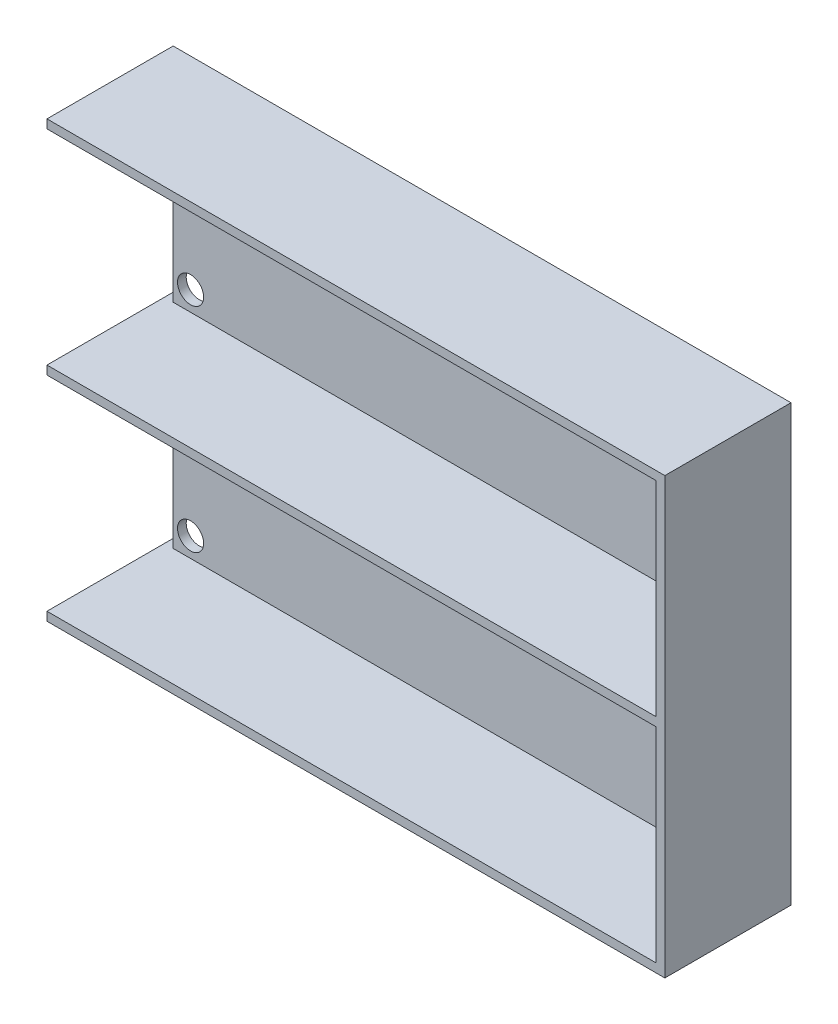
SolidWorks part; units mm, degrees
ref_plane "Front Plane" through (0, 0, 0) normal (0, 0, 1) x (1, 0, 0)
ref_plane "Top Plane" through (0, 0, 0) normal (0, 1, 0) x (1, 0, 0)
ref_plane "Right Plane" through (0, 0, 0) normal (1, 0, 0) x (0, 0, -1)
sketch "Sketch1" plane through (0, 0, 0) normal (0, 0, 1) x (1, 0, 0)
  line L1 (-62.5513, 46.7897) -> (79.4487, 46.7897)
  line L2 (-62.5513, 46.7897) -> (-62.5513, -53.2103)
  line L3 (-62.5513, -53.2103) -> (79.4487, -53.2103)
  line L4 (79.4487, 46.7897) -> (79.4487, -53.2103)
  dimension "D1" = 142
  dimension "D2" = 100
extrude "Boss-Extrude1" add sketch "Sketch1" along normal blind 2
sketch "Sketch3" plane through (0, 0, 2) normal (0, 0, 1) x (1, 0, 0)
  line L0 (79.4487, -53.2103) -> (79.4487, 46.7897) construction
  line L1 (-62.5513, -53.2103) -> (79.4487, -53.2103)
  line L2 (-62.5513, -53.2103) -> (-62.5513, -51.2103)
  line L3 (-62.5513, -51.2103) -> (77.4487, -51.2103)
  line L4 (77.4487, -51.2103) -> (77.4487, -4.2103)
  line L5 (-62.5513, 46.7897) -> (-62.5513, -53.2103) construction
  line L6 (79.4487, 46.7897) -> (-62.5513, 46.7897)
  line L7 (77.4487, -2.2103) -> (77.4487, 44.7897)
  line L8 (77.4487, 44.7897) -> (-62.5513, 44.7897)
  line L9 (-62.5513, 46.7897) -> (-62.5513, 44.7897)
  line L11 (-62.5513, -2.2103) -> (77.4487, -2.2103)
  line L12 (-62.5513, -2.2103) -> (-62.5513, -4.2103)
  line L13 (-62.5513, -4.2103) -> (77.4487, -4.2103)
  line L16 (79.4487, -53.2103) -> (79.4487, 46.7897)
  point P18 (-62.5513, -3.2103)
  point P21 (-62.5513, -3.2103)
  dimension "D1" = 2
  dimension "D2" = 2
  dimension "D3" = 2
  dimension "D4" = 2
extrude "Boss-Extrude2" add sketch "Sketch3" along normal blind 27
sketch "Sketch4" plane through (0, 0, 2) normal (0, 0, 1) x (1, 0, 0)
  line L0 (-62.5513, 44.7897) -> (77.4487, 44.7897) construction
  line L1 (-62.5513, -2.2103) -> (-60.5513, -2.2103)
  line L2 (-62.5513, -2.2103) -> (-62.5513, 44.7897)
  line L3 (-62.5513, 44.7897) -> (-60.5513, 44.7897)
  line L4 (-60.5513, -2.2103) -> (-60.5513, 44.7897)
  line L5 (-62.5513, -4.2103) -> (77.4487, -4.2103) construction
  line L6 (-60.5513, -4.2103) -> (-62.5513, -4.2103)
  line L7 (-60.5513, -4.2103) -> (-60.5513, -51.2103)
  line L8 (-60.5513, -51.2103) -> (-62.5513, -51.2103)
  line L9 (-62.5513, -4.2103) -> (-62.5513, -51.2103)
  dimension "D1" = 2
extrude "Cut-Extrude1" cut sketch "Sketch4" against normal through all
sketch "Sketch5" plane through (0, 0, 0) normal (0, 0, -1) x (-1, 0, 0)
  line L0 (56.5513, 46.7897) -> (56.5513, -53.2103) construction
  line L1 (-79.4487, 46.7897) -> (62.5513, 46.7897) construction
  line L2 (62.5513, -53.2103) -> (-79.4487, -53.2103) construction
  line L3 (62.5513, -3.2103) -> (-79.4487, -3.2103) construction
  line L4 (62.5513, -2.2103) -> (62.5513, -4.2103) construction
  line L5 (-79.4487, -53.2103) -> (-79.4487, 46.7897) construction
  line L6 (62.5513, 46.7897) -> (62.5513, 44.7897) construction
  circle A0 centre (56.5513, 40.2897) radius 3
  circle A1 centre (56.5513, 2.2897) radius 3
  circle A2 centre (56.5513, -8.7103) radius 3
  circle A3 centre (56.5513, -46.7103) radius 3
  dimension "D2" = 6
  dimension "D1" = 6
  dimension "D3" = 6.5
  dimension "D4" = 5.5
  dimension "D5" = 5.5
  dimension "D6" = 6.5
extrude "Cut-Extrude4" cut sketch "Sketch5" against normal through all
